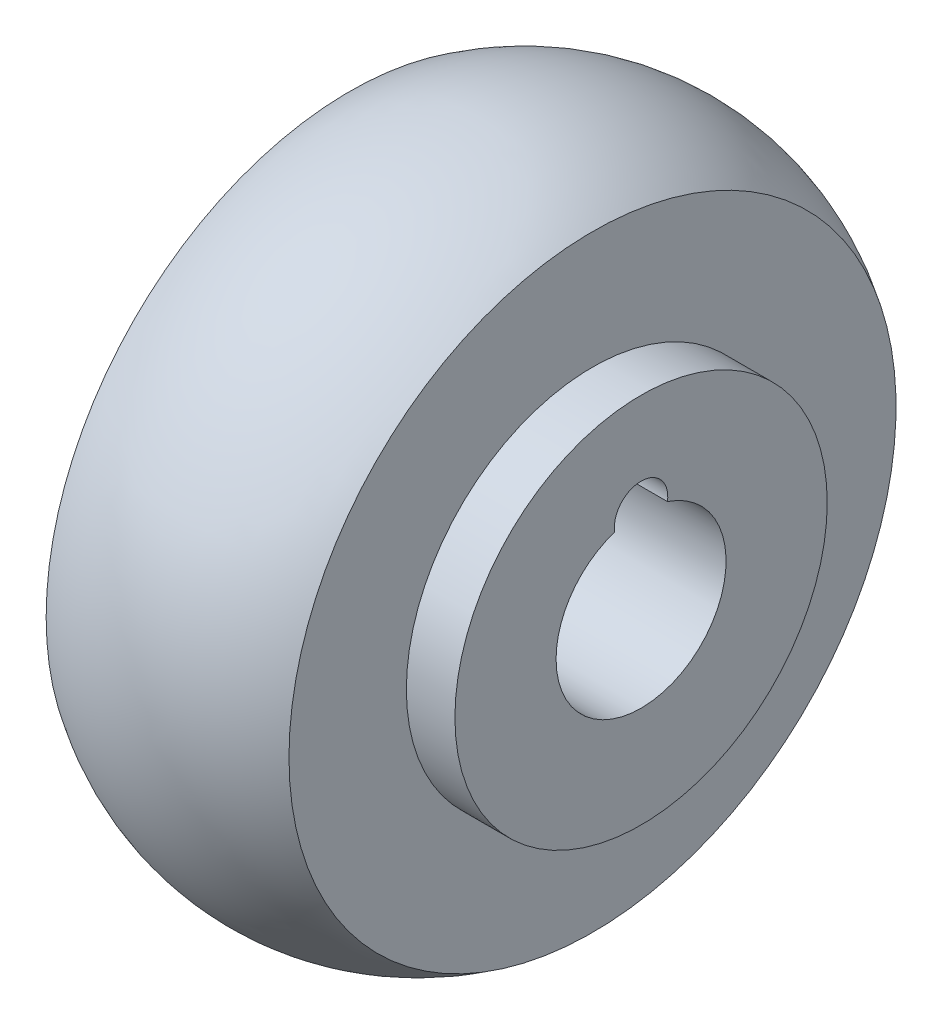
SolidWorks part; units mm, degrees
ref_plane "Front Plane" through (0, 0, 0) normal (0, 0, 1) x (1, 0, 0)
ref_plane "Top Plane" through (0, 0, 0) normal (0, 1, 0) x (1, 0, 0)
ref_plane "Right Plane" through (0, 0, 0) normal (1, 0, 0) x (0, 0, -1)
sketch "Sketch1" plane through (0, 0, 0) normal (0, 1, 0) x (1, 0, 0)
  line L0 (-68.2479, 0) -> (0, 0) construction
  line L1 (-21, 10.5) -> (21, 10.5)
  line L2 (21, 10.5) -> (21, 23)
  line L3 (-21, 10.5) -> (-21, 23)
  line L4 (-21, 23) -> (-15, 23)
  line L5 (-15, 23) -> (-15, 37.5)
  line L6 (-15, 37.5) -> (15, 37.5) construction
  line L7 (15, 37.5) -> (15, 23)
  line L8 (15, 23) -> (21, 23)
  line L9 (0, 0) -> (0, 10.5) construction
  arc A0 (-15, 37.5) -> (15, 37.5) centre (0, 14.75) cw
  point P13 (0, 42)
  dimension "D6" = 42
  dimension "D1" = 10.5
  dimension "D2" = 42
  dimension "D3" = 23
  dimension "D4" = 30
  dimension "D5" = 37.5
revolve "Revolve1" add sketch "Sketch1" angle 360 about L0
hole_wizard "M6 Clearance Hole1" positions "3DSketch2" profile "Sketch3" hole size "M6" standard "ISO"
sketch3d "3DSketch2"
  line L0 (21, -3.2621, 0) -> (21, 8.2882, 0) construction
  circle A0 centre (21, 0, 0) radius 10.5 construction
  point P0 (21, 10.5, 0)
  point P12 (10.5, 0, 0)
sketch "Sketch3" plane through (21, 10.5, 0) normal (0, 1, 0) x (0, 0, -1)
  line L0 (0, 0) -> (0, 12)
  line L1 (0, 12) -> (3.3, 12)
  line L2 (3.3, 12) -> (3.3, 0)
  line L5 (3.3, 0) -> (0, 0)
  line L10 (0, 12) -> (-3.3, 12) construction
  line L11 (0, -6.35) -> (0, 107.95) construction
  dimension "Диаметр отверстия" = 6.6
  dimension "Глубина отверстия" = 12
